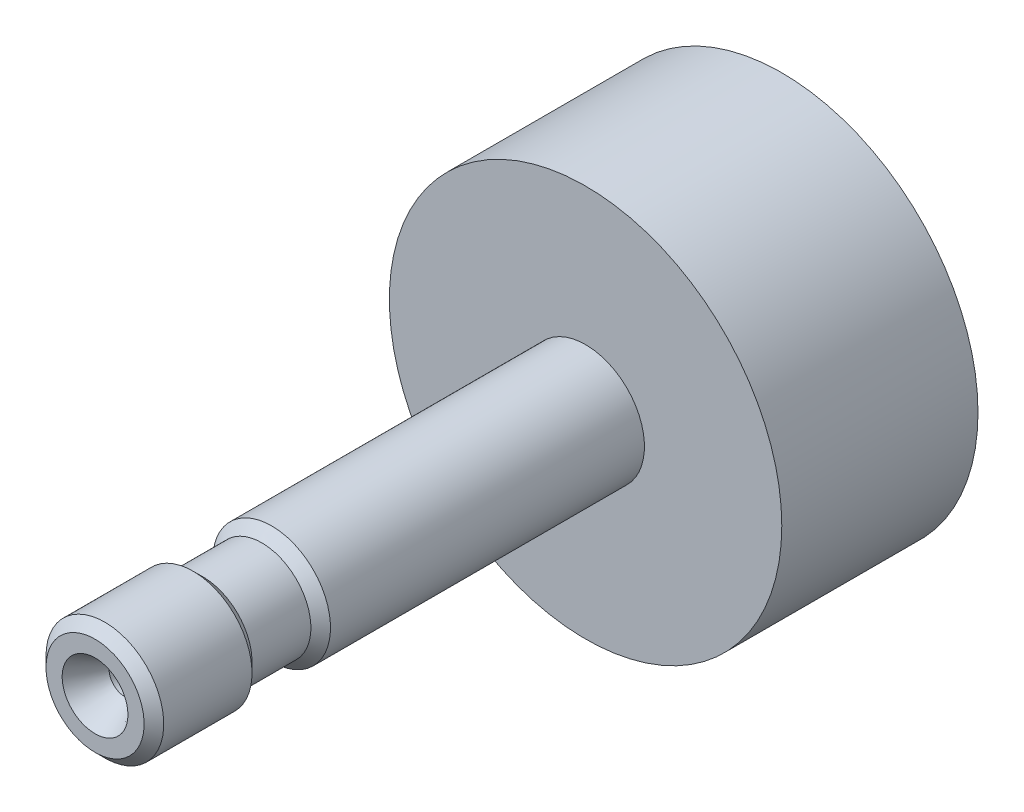
SolidWorks part; units mm, degrees
ref_plane "Ebene vorne" through (0, 0, 0) normal (0, 0, 1) x (1, 0, 0)
ref_plane "Ebene oben" through (0, 0, 0) normal (0, 1, 0) x (1, 0, 0)
ref_plane "Ebene rechts" through (0, 0, 0) normal (1, 0, 0) x (0, 0, -1)
sketch "Skizze1" plane through (0, 0, 0) normal (0, 0, 1) x (1, 0, 0)
  circle A0 centre (0, 0) radius 10
  dimension "D1" = 20
extrude "Aufsatz-Linear Basis (Kann unterschiedliche Formen haben)" add sketch "Skizze1" against normal blind 10
sketch "Skizze2" plane through (0, 0, 0) normal (1, 0, 0) x (0, 0, -1)
  line L0 (0.9378, 0) -> (-35.9436, 0) construction
  line L1 (0, 0) -> (0, 3)
  line L2 (0, 3) -> (-16, 3)
  line L3 (-16, 3) -> (-16.5, 2.5)
  line L4 (-16.5, 2.5) -> (-19.5, 2.5)
  line L5 (-19.5, 2.5) -> (-20, 3)
  line L6 (-20, 3) -> (-24.5, 3)
  line L7 (-24.5, 3) -> (-25, 2.5)
  line L8 (-25, 2.5) -> (-25, 0)
  line L9 (-25, 0) -> (0, 0)
  dimension "D1" = 0.5
  dimension "LängeGesamt" = 25
  dimension "BreiteEinstich" = 4
  dimension "D3" = 45
  dimension "ØGriff" = 6
  dimension "D6" = 0.5
  dimension "LängebisEinstich" = 5
revolve "Lehrengriffstück" add sketch "Skizze2" angle 360 about L0
sketch "Position" plane through (0.1751, -0.1936, 25) normal (0, 0, 1) x (1, 0, 0)
  line L0 (-2.3515, 0.1936) -> (-0.1751, 0.1936) construction
  line L1 (-0.1751, 0.1936) -> (-0.1751, -1.9829) construction
  circle A0 centre (-0.1751, 0.1936) radius 2.1764
  circle A1 centre (-0.1751, 0.1936) radius 2.5 construction
ref_plane "Ebene1" through (0, 0, 25) normal (0, -1, 0) x (1, 0, 0)
sketch "Skizze3" plane through (0, 0, 25) normal (0, -1, 0) x (1, 0, 0)
  line L0 (0, 0) -> (0, -4.7988) construction
  line L2 (0, -3.3807) -> (0.8, -2.9)
  line L3 (0.8, -2.9) -> (0.8, -1.5155)
  line L4 (0.8, -1.5155) -> (1.675, 0)
  line L5 (1.675, 0) -> (0, 0)
  line L6 (0, 0) -> (0, -3.3807)
  dimension "w1" = 30
  dimension "w2" = 59
  dimension "d1" = 1.6
  dimension "d2" = 3.35
  dimension "t1" = 2.9
revolve "Schnitt-Rotation1" cut sketch "Skizze3" angle 360 about L0
